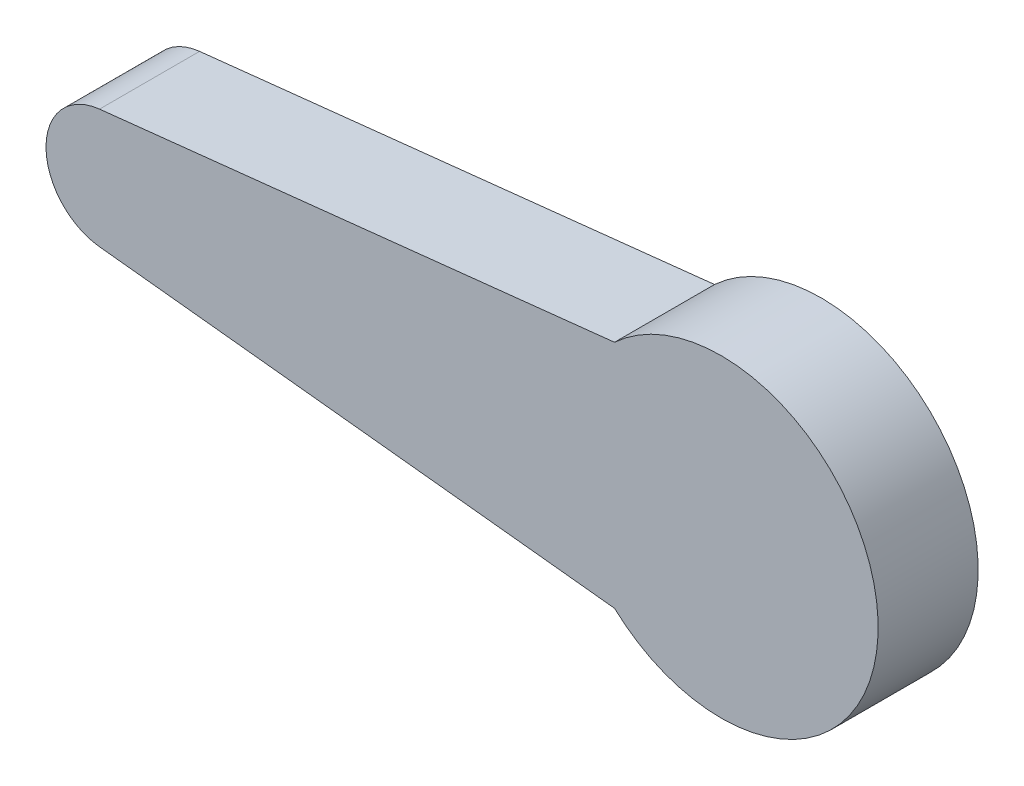
SolidWorks part; units mm, degrees
ref_plane "Front Plane" through (0, 0, 0) normal (0, 0, 1) x (1, 0, 0)
ref_plane "Top Plane" through (0, 0, 0) normal (0, 1, 0) x (1, 0, 0)
ref_plane "Right Plane" through (0, 0, 0) normal (1, 0, 0) x (0, 0, -1)
sketch "Sketch1" plane through (0, 0, 0) normal (0, 0, 1) x (1, 0, 0)
  line L0 (-2.3083, 2.4981) -> (9.375, 3.1901)
  line L1 (9.375, -3.1901) -> (-2.3083, -2.4981)
  spline S0 degree 3 poles (9.375, 3.1901) (9.7438, 3.5351) (10.5421, 3.8854) (11.7399, 4.0538) (12.7816, 3.904) (13.6476, 3.5884) (14.1725, 3.1236) (14.7494, 2.728) (15.2394, 2.0155) (15.6535, 1.0509) (15.789, -0.0007) (15.6517, -1.0481) (15.2469, -2.0252) (14.6033, -2.864) (13.7643, -3.5078) (12.7878, -3.9119) (11.7382, -4.0517) (10.5429, -3.8863) (9.7436, -3.5348) (9.375, -3.1901) knots 0 0 0 0 0.085137 0.144403 0.203669 0.262935 0.297503 0.322201 0.381468 0.440734 0.5 0.559266 0.618532 0.677799 0.737065 0.796331 0.855597 0.914863 1 1 1 1
  spline S1 degree 3 poles (-2.3083, -2.4981) (-2.7303, -2.4987) (-3.3653, -2.3178) (-4.0519, -1.7912) (-4.4545, -1.2665) (-4.7076, -0.6556) (-4.7939, 0) (-4.7076, 0.6556) (-4.4545, 1.2665) (-4.0519, 1.7912) (-3.3653, 2.3178) (-2.7303, 2.4987) (-2.3083, 2.4981) knots 0 0 0 0 0.162547 0.246911 0.331273 0.415637 0.5 0.584363 0.668727 0.753089 0.837453 1 1 1 1
sketch "Sketch2" plane through (0, 0, 0) normal (0, 0, 1) x (1, 0, 0)
  line L1 (7.9369, 4.6075) -> (-12.6575, 2.3846)
  line L4 (-12.6575, -2.3846) -> (7.9369, -4.6075)
  arc A3 (-12.6575, 2.3846) -> (-12.6575, -2.3846) centre (-12.4001, 0) ccw
  arc A4 (7.9369, 4.6075) -> (7.9369, -4.6075) centre (12.2014, 0) cw
  point P1 (-14.7986, 0)
  dimension "D1" = 27
  dimension "D3" = 6.2781
extrude "Boss-Extrude6" add sketch "Sketch2" along normal blind 4 contours A4 L4 A3 L1
extrude "Cut-Extrude1" cut sketch "Sketch1" along normal blind 2
